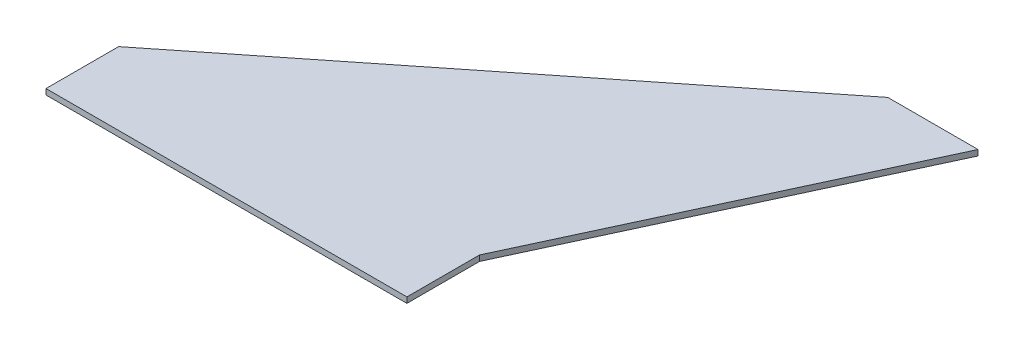
SolidWorks part; units mm, degrees
ref_plane "Front Plane" through (0, 0, 0) normal (0, 0, 1) x (1, 0, 0)
ref_plane "Top Plane" through (0, 0, 0) normal (0, 1, 0) x (1, 0, 0)
ref_plane "Right Plane" through (0, 0, 0) normal (1, 0, 0) x (0, 0, -1)
sketch "Sketch1" plane through (0, 0, 0) normal (0, 1, 0) x (1, 0, 0)
  line L0 (0, 40.894) -> (241.3, 232.664)
  line L1 (0, 0) -> (203.2, 0)
  line L2 (0, 0) -> (0, 40.894)
  line L4 (203.2, 0) -> (203.2, 40.894)
  line L6 (292.1, 232.664) -> (203.2, 40.894)
  line L7 (292.1, 232.664) -> (241.3, 232.664)
  line L8 (0, 40.894) -> (203.2, 40.894) construction
  dimension "D1" = 203.2
  dimension "D2" = 50.8
  dimension "D3" = 191.77
  dimension "D4" = 241.3
  dimension "D6" = 40.894
extrude "Boss-Extrude1" add sketch "Sketch1" along normal blind 3.175
